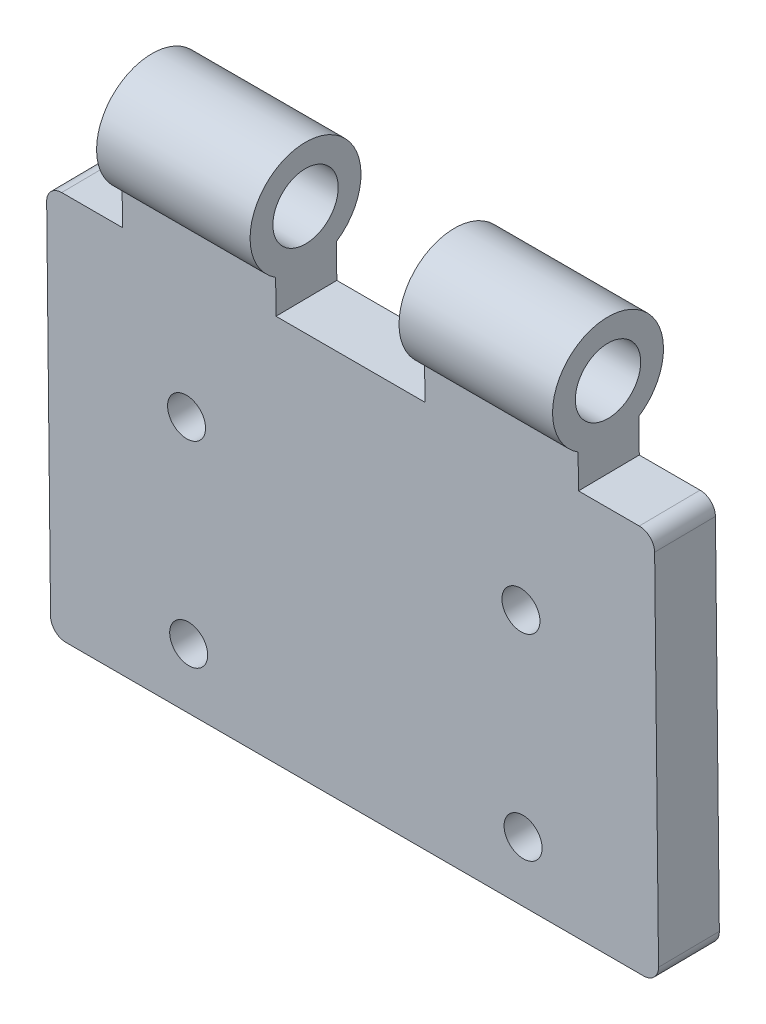
SolidWorks part; units mm, degrees
ref_plane "前视基准面" through (0, 0, 0) normal (0, 0, 1) x (1, 0, 0)
ref_plane "上视基准面" through (0, 0, 0) normal (0, 1, 0) x (1, 0, 0)
ref_plane "右视基准面" through (0, 0, 0) normal (1, 0, 0) x (0, 0, -1)
other "Configuration Table"
sketch "草图1" plane through (0, 0, 0) normal (1, 0, 0) x (0, 0, -1)
  line L1 (-1.9671, -3.0746) -> (-1.6653, -31.0746)
  line L2 (2.0329, -3.0315) -> (2.3347, -31.0315)
  line L3 (-1.6653, -31.0746) -> (2.3347, -31.0315)
  circle A0 centre (0, 0) radius 2.15
  arc A1 (2.0329, -3.0315) -> (-1.9671, -3.0746) centre (0, 0) ccw
  dimension "D1" = 1.5
  dimension "D2" = 7.3
  dimension "D3" = 28
  dimension "D4" = 4
extrude "凸台-拉伸1" add sketch "草图1" along normal blind 40
sketch "草图2" plane through (0, -0.0216, 2) normal (0, -0.0108, 0.9999) x (1, 0, 0)
  line L0 (40, -5.2787) -> (40, -3.0532) construction
  line L1 (40, -3.0532) -> (40, 3.8713) construction
  line L2 (0, -5.2787) -> (0, -3.0532) construction
  line L3 (0, 3.8713) -> (0, -3.0532) construction
  line L4 (5, 4.7213) -> (15.1, 4.7213) construction
  line L5 (5, 4.7213) -> (5, -5.2787) construction
  line L6 (5, -5.2787) -> (15.1, -5.2787) construction
  line L7 (15.1, 4.7213) -> (15.1, -5.2787) construction
  line L8 (10.05, -5.2787) -> (10.05, 4.7213) construction
  line L9 (5, -0.2787) -> (15.1, -0.2787) construction
  line L10 (0, -3.0532) -> (40, -3.0532) construction
  line L11 (20, -19.7475) -> (20, 13.6411) construction
  line L12 (35, -5.2787) -> (24.9, -5.2787) construction
  line L13 (24.9, 4.7213) -> (24.9, -5.2787) construction
  line L14 (35, 4.7213) -> (24.9, 4.7213) construction
  line L15 (35, 4.7213) -> (35, -5.2787) construction
  line L16 (40, -3.0532) -> (0, -3.0532) construction
  line L18 (40, -3.0532) -> (0, -3.0532)
  line L20 (0, -5.2787) -> (5, -5.2787)
  line L21 (0, -5.2787) -> (0, 4.7213)
  line L22 (0, 4.7213) -> (5, 4.7213)
  line L23 (5, -5.2787) -> (5, 4.7213)
  line L24 (15.1, -5.2787) -> (24.9, -5.2787)
  line L25 (15.1, -5.2787) -> (15.1, 4.7213)
  line L26 (15.1, 4.7213) -> (24.9, 4.7213)
  line L27 (24.9, -5.2787) -> (24.9, 4.7213)
  line L28 (40, -5.2787) -> (35, -5.2787)
  line L29 (40, -5.2787) -> (40, 4.7213)
  line L30 (40, 4.7213) -> (35, 4.7213)
  line L31 (35, -5.2787) -> (35, 4.7213)
  point P2 (10.05, -0.2787)
  point P13 (20, -3.0532)
sketch "草图3" plane through (0, 0.0216, -2) normal (0, 0.0108, -0.9999) x (-1, 0, 0)
  line L0 (0, -31.0548) -> (0, -3.0532) construction
  line L1 (-40, -31.0548) -> (-40, -3.0532) construction
  line L2 (-40, -31.0548) -> (0, -31.0548) construction
  line L3 (0, -31.0548) -> (0, -3.0532) construction
  line L4 (-40, -31.0548) -> (-40, -3.0532) construction
  line L5 (-40, -31.0548) -> (0, -31.0548) construction
  line L6 (-20.1201, -31.0548) -> (-20.1201, 12.4638) construction
  circle A0 centre (-31.1201, -27.0548) radius 1.25
  circle A1 centre (-31.1201, -14.0548) radius 1.25
  circle A2 centre (-9.1201, -27.0548) radius 1.25
  circle A3 centre (-9.1201, -14.0548) radius 1.25
  dimension "D3" = 2.5
  dimension "D4" = 2.5
  dimension "D1" = 11
  dimension "D2" = 4
  dimension "D5" = 13
extrude "切除-拉伸2" cut sketch "草图3" against normal up to surface (4.0002 mm away) up to face at (20, -17.0746, 1.8162)
extrude "切除-拉伸3" cut sketch "草图2" against normal mid plane 22 contours L23 L22 L21 L20 | L27 L26 L25 L24 | L29 L30 L31 L28
fillet "圆角1" radius 1 4 edges at (40, -31.053, -0.3347) (0, -31.053, -0.3347) (0, -5.2784, -0.0569) (40, -5.2784, -0.0569)
